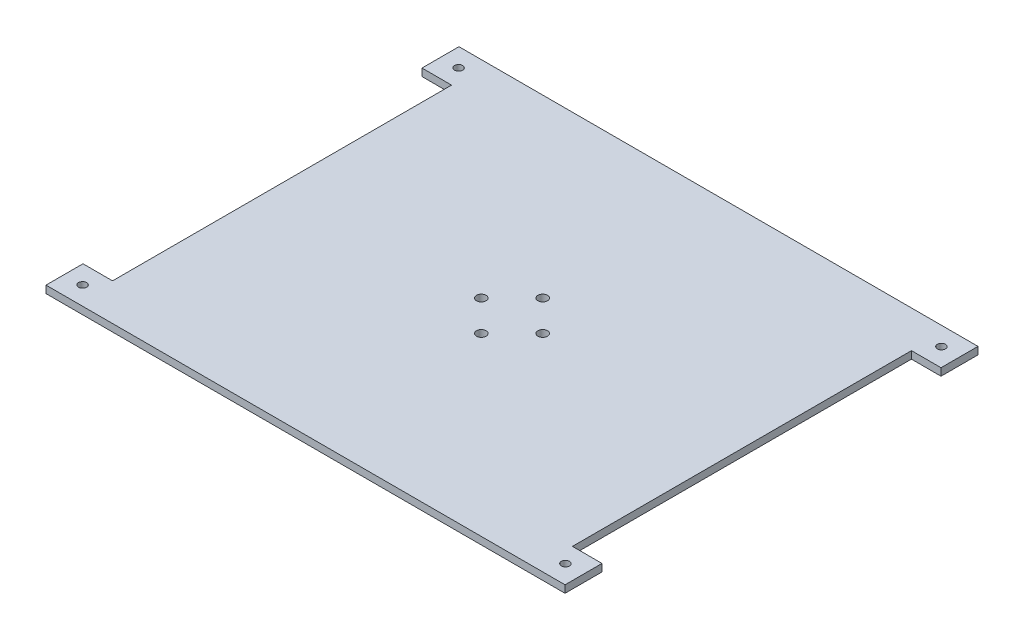
SolidWorks part; units mm, degrees
ref_plane "Front Plane" through (0, 0, 0) normal (0, 0, 1) x (1, 0, 0)
ref_plane "Top Plane" through (0, 0, 0) normal (0, 1, 0) x (1, 0, 0)
ref_plane "Right Plane" through (0, 0, 0) normal (1, 0, 0) x (0, 0, -1)
sketch "Sketch1" plane through (0, 0, 0) normal (0, 1, 0) x (1, 0, 0)
  line L0 (-53.7491, 17.4464) -> (-45.7491, 17.4464)
  line L1 (-53.7491, 27.4464) -> (86.6509, 27.4464)
  line L2 (-53.7491, 17.4464) -> (-53.7491, 27.4464)
  line L3 (-53.7491, -84.2536) -> (86.6509, -84.2536)
  line L4 (86.6509, 17.4464) -> (86.6509, 27.4464)
  line L5 (-45.7491, 17.4464) -> (-45.7491, -74.2536)
  line L6 (-45.7491, -74.2536) -> (-53.7491, -74.2536)
  line L7 (-53.7491, -74.2536) -> (-53.7491, -84.2536)
  line L8 (78.6509, 17.4464) -> (86.6509, 17.4464)
  line L9 (78.6509, -74.2536) -> (86.6509, -74.2536)
  line L10 (78.6509, 17.4464) -> (78.6509, -74.2536)
  line L11 (86.6509, -84.2536) -> (86.6509, -74.2536)
  point P4 (86.6509, 17.4464)
  point P5 (86.6509, -74.2536)
  point P6 (-53.7491, 17.4464)
  point P7 (-53.7491, -74.2536)
  point P8 (-45.7491, 17.4464)
  point P9 (78.6509, 17.4464)
  point P10 (78.6509, -74.2536)
  point P11 (-45.7491, -74.2536)
  dimension "D1" = 140.4
  dimension "D2" = 111.7
  dimension "D3" = 10
  dimension "D4" = 10
  dimension "D5" = 10
  dimension "D6" = 10
  dimension "D7" = 8
  dimension "D8" = 8
  dimension "D9" = 8
  dimension "D10" = 8
extrude "Boss-Extrude1" add sketch "Sketch1" along normal blind 2
sketch "Sketch2" plane through (0, 2, 0) normal (0, 1, 0) x (1, 0, 0)
  line L0 (86.6509, -84.2536) -> (86.6509, -74.2536) construction
  line L1 (86.6509, 17.4464) -> (86.6509, 27.4464) construction
  line L2 (-53.7491, 27.4464) -> (-53.7491, 17.4464) construction
  line L3 (-53.7491, -74.2536) -> (-53.7491, -84.2536) construction
  circle A0 centre (-48.8491, -79.2536) radius 1.1
  circle A1 centre (-48.8491, 22.4464) radius 1.1
  circle A2 centre (81.7509, 22.4464) radius 1.1
  circle A3 centre (81.7509, -79.2536) radius 1.1
  point P0 (86.6509, -79.2536)
  point P1 (81.7509, -79.2536)
  point P4 (86.6509, 22.4464)
  point P5 (81.7509, 22.4464)
  point P8 (-53.7491, 22.4464)
  point P9 (-48.8491, 22.4464)
  point P12 (-53.7491, -79.2536)
  point P13 (-48.8491, -79.2536)
  dimension "D1" = 4.9
  dimension "D2" = 4.9
  dimension "D3" = 4.9
  dimension "D4" = 4.9
extrude "Cut-Extrude1" cut sketch "Sketch2" against normal blind 2
sketch "Sketch3" plane through (0, 2, 0) normal (0, 1, 0) x (1, 0, 0)
  line L0 (-53.7491, -84.2536) -> (86.6509, -84.2536) construction
  line L1 (-45.7491, 17.4464) -> (-45.7491, -74.2536) construction
  circle A0 centre (8.1509, -28.4036) radius 1.3
  circle A1 centre (16.4509, -36.7036) radius 1.3
  circle A2 centre (24.7509, -28.4036) radius 1.3
  circle A3 centre (16.4509, -20.1036) radius 1.3
  point P0 (16.4509, -84.2536)
  point P1 (16.4509, -28.4036)
  point P4 (-45.7491, -28.4036)
  point P5 (8.1509, -28.4036)
  point P8 (24.7509, -28.4036)
  point P9 (16.4509, -20.1036)
  point P10 (16.4509, -36.7036)
  dimension "D1" = 8.3
  dimension "D2" = 8.3
  dimension "D3" = 8.3
  dimension "D4" = 8.3
extrude "Cut-Extrude2" cut sketch "Sketch3" against normal blind 2
